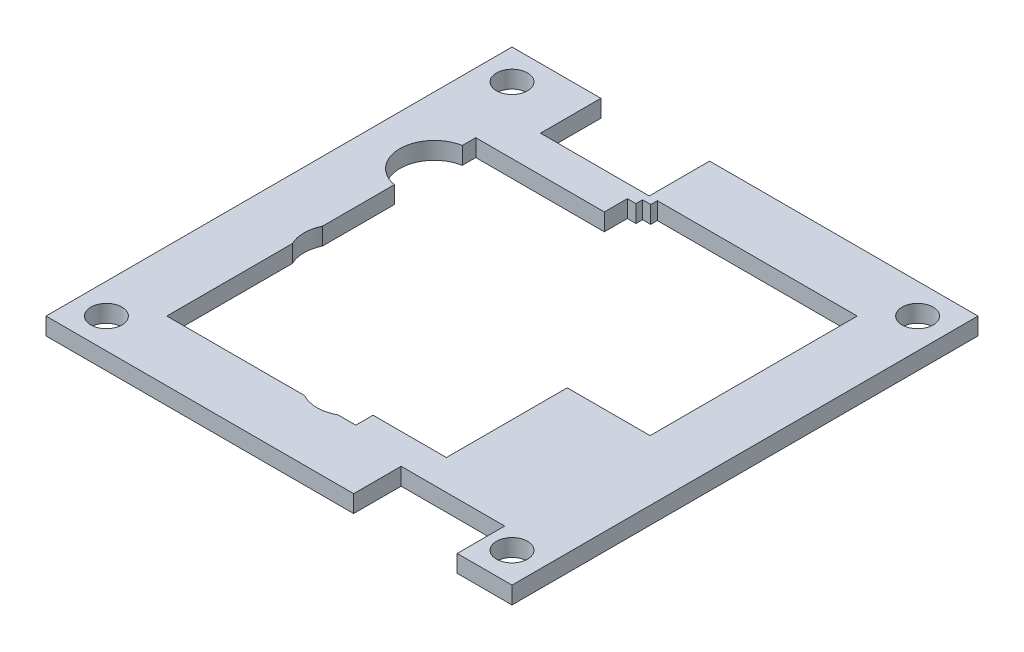
SolidWorks part; units mm, degrees
ref_plane "Front" through (0, 0, 0) normal (0, 0, 1) x (1, 0, 0)
ref_plane "Top" through (0, 0, 0) normal (0, 1, 0) x (1, 0, 0)
ref_plane "Right" through (0, 0, 0) normal (1, 0, 0) x (0, 0, -1)
sketch "草图3" plane through (0, 0, 0) normal (0, 1, 0) x (1, 0, 0)
  line L0 (16.9, -20) -> (20, -20)
  line L1 (-20, -20) -> (12.4, -20)
  line L2 (20, -20) -> (20, 20)
  line L3 (-27, 27) -> (-27, -27)
  line L4 (-27, -27) -> (27, -27)
  line L5 (27, -27) -> (27, 27)
  line L6 (27, 27) -> (-27, 27)
  line L7 (-8.6, 1.7) -> (-7.6812, 1.7)
  line L8 (-5.8437, 1.7) -> (-4.925, 1.7)
  line L9 (20.65, -20) -> (20, -20)
  line L10 (16.9, -6) -> (12.4, -6)
  line L11 (12.4, -6) -> (12.4, -19.5)
  line L12 (-10.4, 20) -> (-4.1, 20)
  line L13 (16.9, -6) -> (16.9, -19.5)
  line L14 (-20, 20) -> (-20, -20)
  line L15 (-3.0875, 1.7) -> (-2.1687, 1.7)
  line L16 (-0.3312, 1.7) -> (0.5875, 1.7)
  line L17 (2.425, 1.7) -> (3.3438, 1.7)
  line L18 (5.1813, 1.7) -> (6.1, 1.7)
  line L19 (8.8563, -13.3) -> (7.9375, -13.3)
  line L20 (8.65, -20) -> (8.65, -27)
  line L21 (-8.6, 1.7) -> (-8.6, -13.3)
  line L22 (-7.6812, -13.3) -> (-8.6, -13.3)
  line L23 (-8.6, -13.3) -> (-8.6029, -13.3589)
  line L24 (-10.4375, -13.3) -> (-11.3562, -13.3)
  line L25 (-10.4375, 1.7) -> (-11.3562, 1.7)
  line L26 (6.1, 1.7) -> (6.1, -13.3)
  line L27 (-4.925, -13.3) -> (-4.925, 1.7)
  line L28 (-11.3562, -13.3) -> (-11.3562, 1.7)
  line L29 (-3.0875, -13.3) -> (-3.0875, 1.7)
  line L30 (-10.4375, -13.3) -> (-10.4375, 1.7)
  line L31 (-2.1687, -13.3) -> (-2.1687, 1.7)
  line L32 (8.8563, 1.7) -> (7.9375, 1.7)
  line L33 (-5.8437, -13.3) -> (-5.8437, 1.7)
  line L34 (8.8563, -13.3) -> (8.8563, 1.7)
  line L35 (-7.6812, -13.3) -> (-7.6812, 1.7)
  line L36 (-0.3312, -13.3) -> (-0.3312, 1.7)
  line L37 (0.5875, -13.3) -> (0.5875, 1.7)
  line L38 (5.1813, -13.3) -> (6.1, -13.3)
  line L39 (2.425, -13.3) -> (2.425, 1.7)
  line L40 (3.3438, -13.3) -> (3.3438, 1.7)
  line L41 (2.425, -13.3) -> (3.3438, -13.3)
  line L42 (5.1813, -13.3) -> (5.1813, 1.7)
  line L43 (-0.3312, -13.3) -> (0.5875, -13.3)
  line L44 (-3.0875, -13.3) -> (-2.1687, -13.3)
  line L45 (-5.8437, -13.3) -> (-4.925, -13.3)
  line L46 (7.9375, -13.3) -> (7.9375, 1.7)
  line L47 (20.65, -20) -> (20.65, -27)
  line L48 (12.4, -19.5) -> (12.4, -20)
  line L49 (16.9, -19.5) -> (16.9, -20)
  line L50 (-20, -20) -> (20, -20) construction
  line L51 (-20, 20) -> (20, 20)
  line L52 (-16.7, 20) -> (-10.4, 20)
  line L53 (20, 20) -> (-20, 20) construction
  line L54 (-16.7, 20) -> (-16.7, 27)
  line L55 (-4.1, 20) -> (-4.1, 27)
  line L56 (12.4, -19.5) -> (16.9, -19.5)
  line L57 (1.9, -18) -> (12.4, -18)
  line L58 (8.65, -21.5) -> (20.65, -21.5)
  line L59 (1.9, -20) -> (1.9, -18)
  line L60 (16.9, -18) -> (16.1, -18)
  line L61 (16.9, -18) -> (20, -18)
  line L62 (12.4, -18) -> (13.4, -18)
  line L63 (13.4, -18) -> (13.4, -19.5)
  line L64 (16.1, -18) -> (16.1, -19.5)
  line L65 (-20, 15.8) -> (-5.1, 15.8)
  line L66 (10.4, -6) -> (10.4, -18)
  line L67 (10.4, -6) -> (10.4, -4)
  line L68 (-5.1, 15.8) -> (-5.1, 18.4633)
  line L69 (10.4, -4) -> (20, -4)
  line L70 (-5.1, 18.4633) -> (-4.1, 18.4633)
  line L71 (-4.1, 18.4633) -> (-4.1, 20)
  line L72 (-4.1, 19.2317) -> (-3.1551, 19.2317)
  line L73 (-3.1551, 19.2317) -> (-3.1551, 20)
  circle A0 centre (-23.5, -23.5) radius 1.8
  circle A1 centre (23.5, -23.5) radius 1.8
  circle A2 centre (-23.5, 23.5) radius 1.8
  circle A3 centre (23.5, 23.5) radius 1.8
  circle A4 centre (-2.1, -16.5) radius 2
  circle A5 centre (-16.4, -3.7) radius 2
  circle A6 centre (-19.3, 10.3) radius 2
  circle A7 centre (-1.1, 15.8) radius 2
  circle A8 centre (-19.3, 10.3) radius 4
  circle A9 centre (-2.1, -16.5) radius 4
  circle A10 centre (-1.1, 15.8) radius 4
  circle A11 centre (-16.4, -3.7) radius 4
  point P0 (0, 0)
  point P61 (-10.8969, 1.7)
  dimension "D1" = 7
extrude "凸台-拉伸2" add sketch "草图3" along normal blind 2 contours A11 L14 A8 L51 L54 L6 L3 L4 L20 L1 A9 A2 A0 | L55 L51 L2 L9 L47 L4 L5 L6 A3 A1 | L59 L1 L48 L11 L57 | L20 L58 L47 L9 L0 L49 L56 L48 L1 | L61 L13 L49 L0 L2 | L60 L64 L56 L13 | L63 L62 L11 L56 | L64 L60 L13 L10 L11 L62 L63 L56 | L69 L67 L66 L57 L11 L10 L13 L61 L2 | L72 L73 L51 L71 | L70 L71 L12 L51 L14 L65 L68
